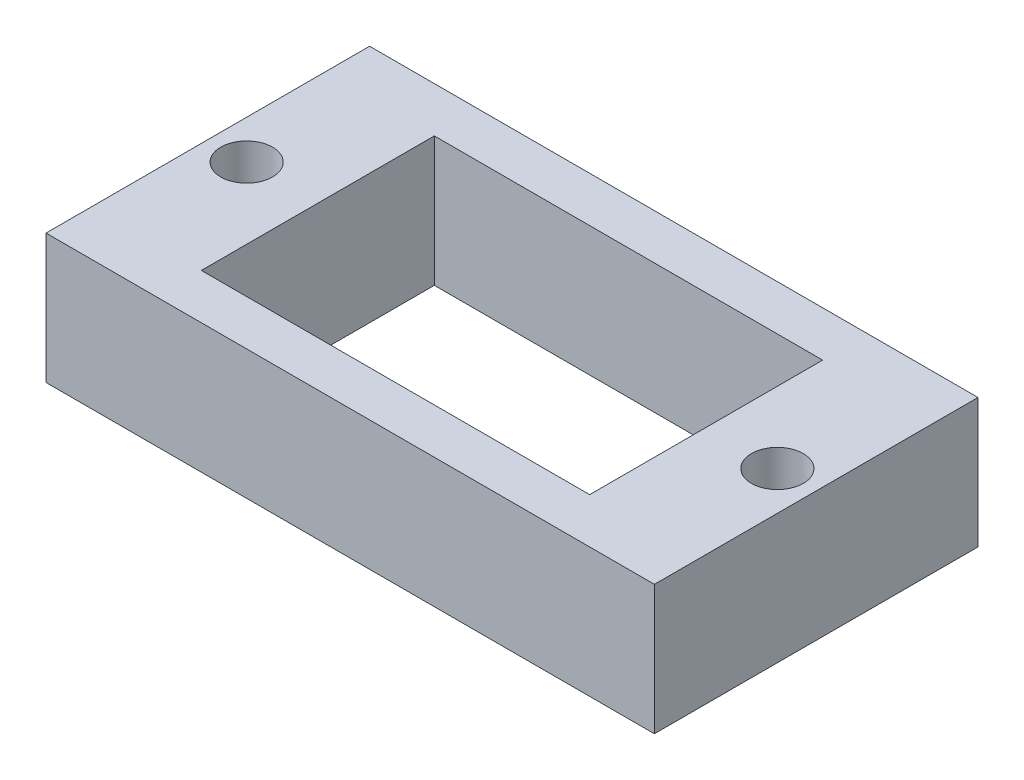
SolidWorks part; units mm, degrees
material "PP Copolymer"
ref_plane "Front Plane" through (0, 0, 0) normal (0, 0, 1) x (1, 0, 0)
ref_plane "Top Plane" through (0, 0, 0) normal (0, 1, 0) x (1, 0, 0)
ref_plane "Right Plane" through (0, 0, 0) normal (1, 0, 0) x (0, 0, -1)
sketch "Sketch1" plane through (0, 0, 0) normal (0, 1, 0) x (1, 0, 0)
  line L1 (0, 0) -> (47, 0)
  line L2 (0, 0) -> (0, 25)
  line L3 (0, 25) -> (47, 25)
  line L4 (47, 0) -> (47, 25)
  dimension "D1" = 25
  dimension "D2" = 47
extrude "Boss-Extrude1" add sketch "Sketch1" along normal blind 10
sketch "Sketch2" plane through (0, 10, 0) normal (0, 1, 0) x (1, 0, 0)
  line L0 (0, 12.5) -> (3, 12.5) construction
  line L1 (0, 25) -> (0, 0) construction
  line L2 (23.5, 25) -> (23.5, 0) construction
  line L3 (47, 25) -> (0, 25) construction
  line L4 (0, 0) -> (47, 0) construction
  circle A0 centre (3, 12.5) radius 2
  circle A1 centre (44, 12.5) radius 2
  dimension "D2" = 4
  dimension "D1" = 3
extrude "Cut-Extrude1" cut sketch "Sketch2" against normal blind 8
sketch "Sketch5" plane through (0, 10, 0) normal (0, 1, 0) x (1, 0, 0)
  line L0 (23.5, 21.5) -> (23.5, 25) construction
  line L1 (8.5, 21.5) -> (38.5, 21.5)
  line L2 (8.5, 21.5) -> (8.5, 3.5)
  line L3 (8.5, 3.5) -> (38.5, 3.5)
  line L4 (38.5, 21.5) -> (38.5, 3.5)
  line L5 (47, 25) -> (0, 25) construction
  line L6 (38.5, 12.5) -> (47, 12.5) construction
  line L7 (47, 0) -> (47, 25) construction
  line L8 (23.5, 3.5) -> (23.5, 0) construction
  line L9 (0, 0) -> (47, 0) construction
  line L10 (8.5, 12.5) -> (0, 12.5) construction
  line L11 (0, 25) -> (0, 0) construction
  dimension "D1" = 30
  dimension "D2" = 18
extrude "Cut-Extrude2" cut sketch "Sketch5" against normal blind 10
